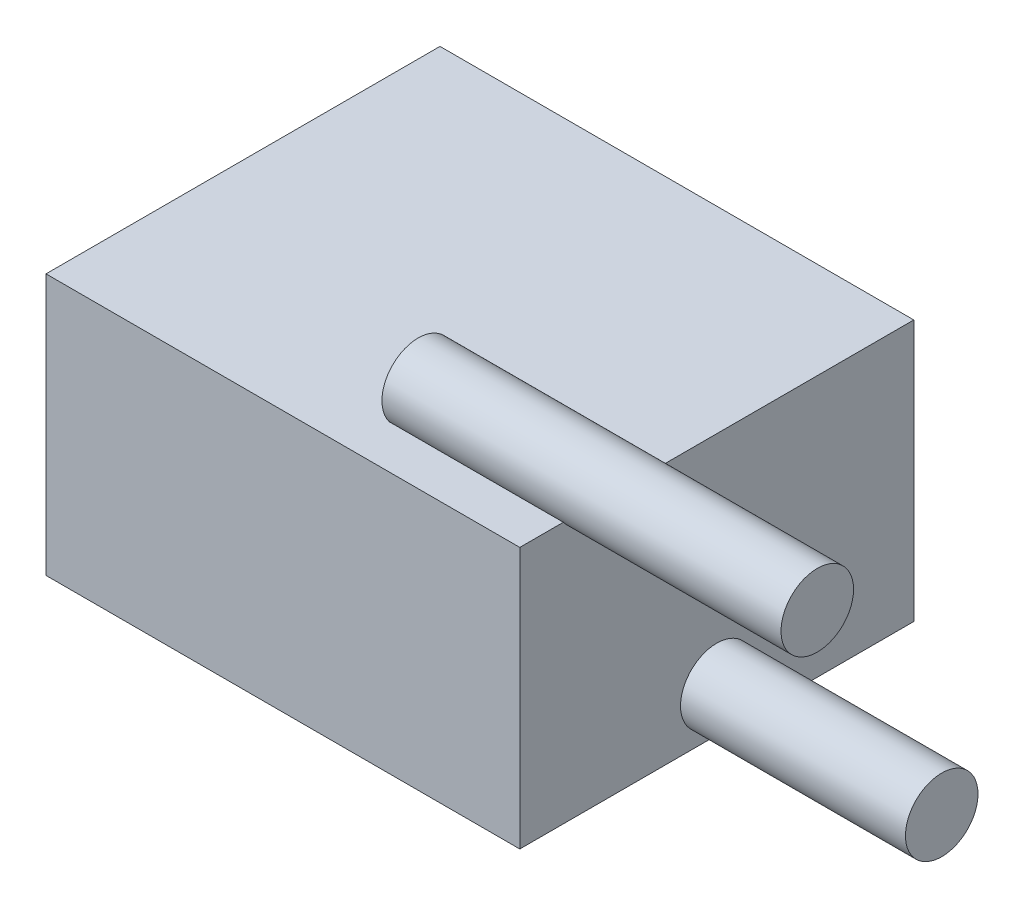
SolidWorks part; units mm, degrees
ref_plane "Front Plane" through (0, 0, 0) normal (0, 0, 1) x (1, 0, 0)
ref_plane "Top Plane" through (0, 0, 0) normal (0, 1, 0) x (1, 0, 0)
ref_plane "Right Plane" through (0, 0, 0) normal (1, 0, 0) x (0, 0, -1)
sketch "Sketch1" plane through (0, 0, 0) normal (0, 1, 0) x (1, 0, 0)
  line L1 (8.2931, -6.8961) -> (-8.2931, -6.8961)
  line L2 (8.2931, -6.8961) -> (8.2931, 6.8961)
  line L3 (8.2931, 6.8961) -> (-8.2931, 6.8961)
  line L4 (-8.2931, -6.8961) -> (-8.2931, 6.8961)
  line L5 (8.2931, -6.8961) -> (-8.2931, 6.8961) construction
  line L6 (8.2931, 6.8961) -> (-8.2931, -6.8961) construction
  point P0 (0, 0)
  dimension "D1" = 13.7922
  dimension "D2" = 16.5862
extrude "Boss-Extrude1" add sketch "Sketch1" along normal blind 9.144
sketch "Sketch2" plane through (8.2931, 0, 0) normal (1, 0, 0) x (0, 0, -1)
  line L0 (-6.8961, 0) -> (6.8961, 0) construction
  line L1 (-6.8961, 9.144) -> (-6.8961, 0) construction
  line L2 (-6.8961, 9.144) -> (6.8961, 9.144) construction
  circle A0 centre (0, 1.524) radius 1.27
  circle A1 centre (-4.3561, 9.906) radius 1.27
  dimension "D1" = 2.54
  dimension "D2" = 1.524
  dimension "D3" = 2.54
  dimension "D4" = 0.762
extrude "Boss-Extrude2" add sketch "Sketch2" along normal blind 7.874 and the other way blind 6.096
